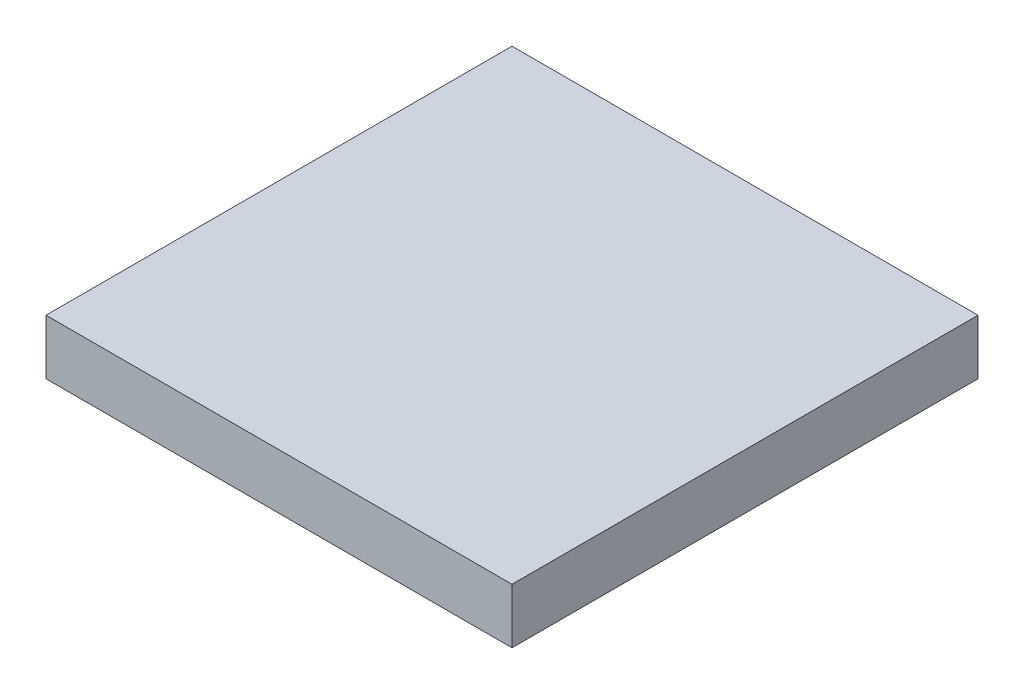
SolidWorks part; units mm, degrees
ref_plane "前视基准面" through (0, 0, 0) normal (0, 0, 1) x (1, 0, 0)
ref_plane "上视基准面" through (0, 0, 0) normal (0, 1, 0) x (1, 0, 0)
ref_plane "右视基准面" through (0, 0, 0) normal (1, 0, 0) x (0, 0, -1)
sketch "草图1" plane through (0, 0, 0) normal (0, 1, 0) x (1, 0, 0)
  line L1 (-6.35, -6.35) -> (6.35, -6.35)
  line L2 (-6.35, -6.35) -> (-6.35, 6.35)
  line L3 (-6.35, 6.35) -> (6.35, 6.35)
  line L4 (6.35, -6.35) -> (6.35, 6.35)
  line L5 (-6.35, -6.35) -> (6.35, 6.35) construction
  line L6 (-6.35, 6.35) -> (6.35, -6.35) construction
  point P0 (0, 0)
  dimension "D1" = 12.7
  dimension "D2" = 12.7
extrude "凸台-拉伸1" add sketch "草图1" along normal blind 1.5
